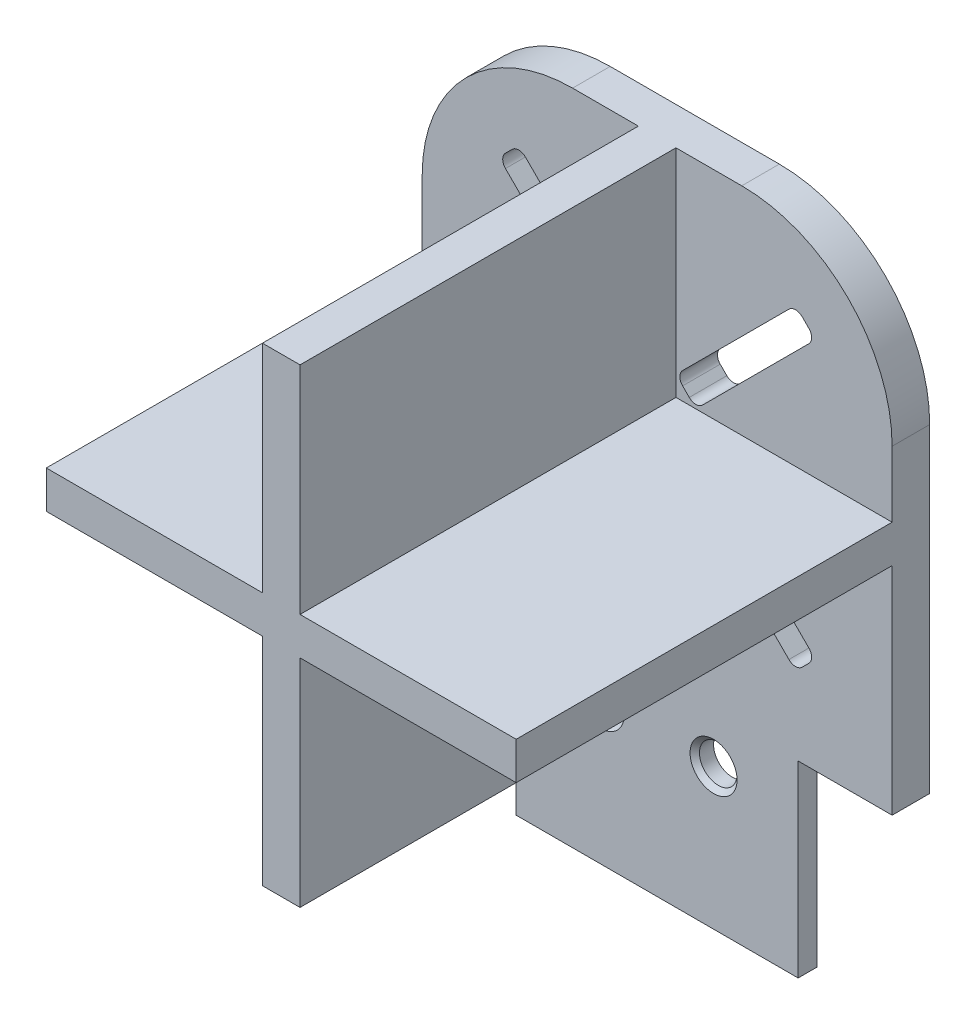
SolidWorks part; units mm, degrees
ref_plane "Płaszczyzna przednia" through (0, 0, 0) normal (0, 0, 1) x (1, 0, 0)
ref_plane "Płaszczyzna górna" through (0, 0, 0) normal (0, 1, 0) x (1, 0, 0)
ref_plane "Płaszczyzna prawa" through (0, 0, 0) normal (1, 0, 0) x (0, 0, -1)
sketch "Szkic2" plane through (0, 0, 0) normal (0, 0, 1) x (1, 0, 0)
  line L1 (0, 0) -> (25, 0)
  line L2 (0, 0) -> (0, -25)
  line L3 (0, -25) -> (25, -25)
  line L4 (25, 0) -> (25, -25)
  dimension "D1" = 25
  dimension "D2" = 25
extrude "Dodanie-wyciągnięcie1" add sketch "Szkic2" along normal blind 2
sketch "Szkic3" plane through (0, 0, 2) normal (0, 0, 1) x (1, 0, 0)
  line L0 (12.5, 0) -> (12.5, -25) construction
  line L2 (0, -25) -> (25, -25) construction
  line L3 (25, -25) -> (25, 0) construction
  line L4 (11.5, 0) -> (13.5, 0)
  line L5 (11.5, 0) -> (11.5, -11.5)
  line L6 (11.5, -25) -> (13.5, -25)
  line L7 (13.5, 0) -> (13.5, -11.5)
  line L8 (11.5, 0) -> (13.5, -25) construction
  line L9 (11.5, -25) -> (13.5, 0) construction
  line L10 (0, -11.5) -> (11.5, -11.5)
  line L11 (0, -11.5) -> (0, -13.5)
  line L12 (0, -13.5) -> (11.5, -13.5)
  line L13 (25, -11.5) -> (25, -13.5)
  line L14 (12.5, -12.5) -> (25, -13.5) construction
  line L15 (12.5, -12.5) -> (25, -11.5) construction
  line L17 (11.5, -13.5) -> (11.5, -25)
  line L18 (13.5, -13.5) -> (25, -13.5)
  line L19 (13.5, -11.5) -> (25, -11.5)
  line L20 (13.5, -13.5) -> (13.5, -25)
  point P6 (12.5, -12.5)
  point P12 (12.5, -12.5)
  dimension "D1" = 2
  dimension "D2" = 2
extrude "Dodanie-wyciągnięcie2" add sketch "Szkic3" along normal blind 20
fillet "Zaokrąglenie1" radius 8 2 edges at (25, 0, 1) (0, 0, 1)
sketch "Szkic7" plane through (0, 0, 2) normal (0, 0, 1) x (1, 0, 0)
  line L0 (10.4393, -13.5) -> (11.5, -14.5607)
  line L1 (10.4393, -13.5) -> (4.0754, -19.864)
  line L2 (11.5, -14.5607) -> (5.136, -20.9246)
  line L3 (4.0754, -19.864) -> (5.136, -20.9246)
  line L4 (10.4393, -13.5) -> (5.136, -20.9246) construction
  line L5 (11.5, -14.5607) -> (4.0754, -19.864) construction
  line L6 (0, -13.5) -> (11.5, -13.5) construction
  line L7 (11.5, -13.5) -> (11.5, -25) construction
  point P6 (7.7877, -17.2123)
  dimension "D1" = 45
  dimension "D2" = 1.5
  dimension "D3" = 9
extrude "Wytnij-wyciągnięcie1" cut sketch "Szkic7" against normal blind 20
fillet "Zaokrąglenie2" radius 0.5 4 edges at (5.136, -20.9246, 1) (4.0754, -19.864, 1) (11.5, -14.5607, 1) (10.4393, -13.5, 1)
sketch "Szkic9" plane through (0, 0, 2) normal (0, 0, 1) x (1, 0, 0)
  line L0 (11.5, -10.4393) -> (10.4393, -11.5)
  line L1 (11.5, -10.4393) -> (5.136, -4.0754)
  line L2 (10.4393, -11.5) -> (4.0754, -5.136)
  line L3 (5.136, -4.0754) -> (4.0754, -5.136)
  line L4 (11.5, -10.4393) -> (4.0754, -5.136) construction
  line L5 (10.4393, -11.5) -> (5.136, -4.0754) construction
  line L6 (11.5, 0) -> (11.5, -11.5) construction
  line L7 (11.5, -11.5) -> (0, -11.5) construction
  point P6 (7.7877, -7.7877)
  dimension "D1" = 1.5
  dimension "D2" = 45
  dimension "D3" = 9
extrude "Wytnij-wyciągnięcie2" cut sketch "Szkic9" against normal blind 20
sketch "Szkic11" plane through (0, 0, 2) normal (0, 0, 1) x (1, 0, 0)
  line L0 (13.5, -10.4393) -> (14.5607, -11.5)
  line L1 (13.5, -10.4393) -> (19.864, -4.0754)
  line L2 (14.5607, -11.5) -> (20.9246, -5.136)
  line L3 (19.864, -4.0754) -> (20.9246, -5.136)
  line L4 (13.5, -10.4393) -> (20.9246, -5.136) construction
  line L5 (14.5607, -11.5) -> (19.864, -4.0754) construction
  line L6 (13.5, -11.5) -> (13.5, 0) construction
  line L7 (25, -11.5) -> (13.5, -11.5) construction
  point P6 (17.2123, -7.7877)
  dimension "D1" = 45
  dimension "D2" = 1.5
  dimension "D3" = 9
extrude "Wytnij-wyciągnięcie3" cut sketch "Szkic11" against normal blind 20
sketch "Szkic12" plane through (0, 0, 2) normal (0, 0, 1) x (1, 0, 0)
  line L0 (14.5607, -13.5) -> (13.5, -14.5607)
  line L1 (14.5607, -13.5) -> (20.9246, -19.864)
  line L2 (13.5, -14.5607) -> (19.864, -20.9246)
  line L3 (20.9246, -19.864) -> (19.864, -20.9246)
  line L4 (14.5607, -13.5) -> (19.864, -20.9246) construction
  line L5 (13.5, -14.5607) -> (20.9246, -19.864) construction
  line L6 (13.5, -13.5) -> (25, -13.5) construction
  line L7 (13.5, -25) -> (13.5, -13.5) construction
  point P6 (17.2123, -17.2123)
  dimension "D1" = 9
  dimension "D2" = 1.5
  dimension "D3" = 45
extrude "Wytnij-wyciągnięcie4" cut sketch "Szkic12" against normal blind 20
fillet "Zaokrąglenie3" radius 0.5 12 edges at (4.0754, -5.136, 1) (5.136, -4.0754, 1) (11.5, -10.4393, 1) (10.4393, -11.5, 1) (19.864, -20.9246, 1) (20.9246, -19.864, 1) (20.9246, -5.136, 1) (19.864, -4.0754, 1) (14.5607, -11.5, 1) (13.5, -10.4393, 1) (13.5, -14.5607, 1) (14.5607, -13.5, 1)
sketch "Szkic14" plane through (0, 0, 2) normal (0, 0, 1) x (1, 0, 0)
  line L0 (0, -25) -> (11.5, -25) construction
  line L1 (5, -25) -> (20, -25)
  line L2 (5, -25) -> (5, -35)
  line L3 (5, -35) -> (20, -35)
  line L4 (20, -25) -> (20, -35)
  line L5 (0, -13.5) -> (0, -25) construction
  dimension "D1" = 15
  dimension "D2" = 10
  dimension "D3" = 5
extrude "Dodanie-wyciągnięcie3" add sketch "Szkic14" against normal blind 1
sketch "Szkic13" plane through (0, 0, 2) normal (0, 0, 1) x (1, 0, 0)
  line L0 (11.5, -13.5) -> (11.5, -25) construction
  line L1 (13.5, -25) -> (11.5, -25) construction
  line L2 (13.5, -25) -> (13.5, -14.5607) construction
  line L3 (13.5, -25) -> (11.5, -25) construction
  circle A0 centre (9.5, -27.5) radius 1
  circle A1 centre (15.5, -27.5) radius 1
  dimension "D1" = 2
  dimension "D2" = 2
  dimension "D3" = 2.5
  dimension "D4" = 2
  dimension "D5" = 2
  dimension "D6" = 2.5
extrude "Wytnij-wyciągnięcie5" cut sketch "Szkic13" against normal blind 1
chamfer "Sfazowanie1" distance 0.25 angle 45 2 edges at (16.5, -27.5, 2) (10.5, -27.5, 2)
